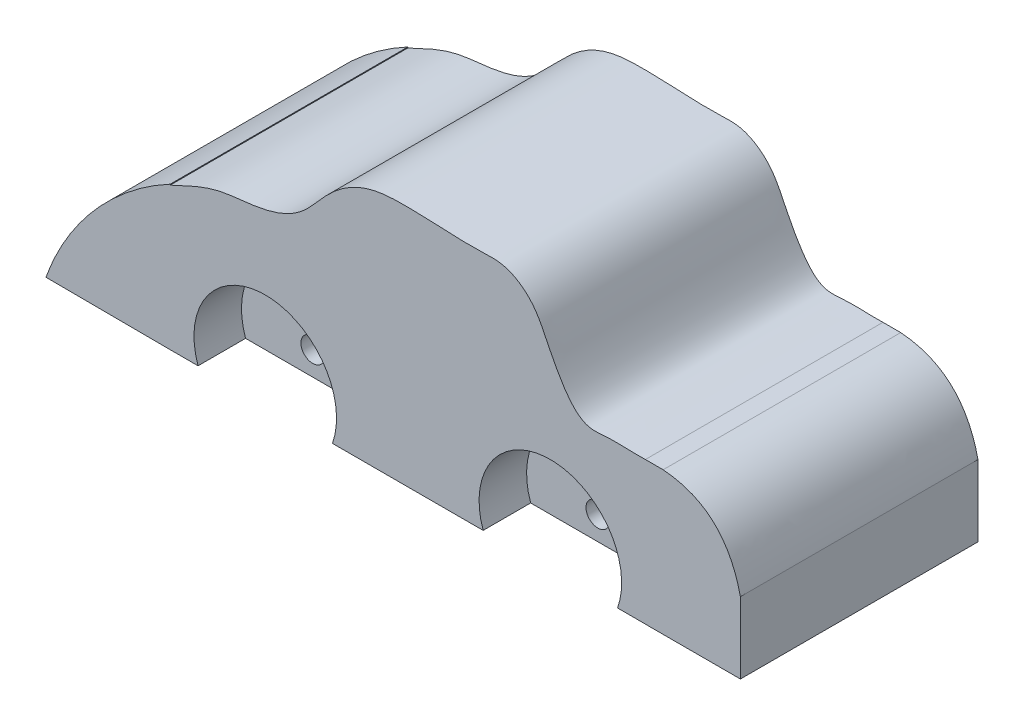
SolidWorks part; units mm, degrees
ref_plane "Front Plane" through (0, 0, 0) normal (0, 0, 1) x (1, 0, 0)
ref_plane "Top Plane" through (0, 0, 0) normal (0, 1, 0) x (1, 0, 0)
ref_plane "Right Plane" through (0, 0, 0) normal (1, 0, 0) x (0, 0, -1)
sketch "Sketch1" plane through (0, 0, 0) normal (0, 1, 0) x (1, 0, 0)
  line L1 (127, -63.5) -> (-127, -63.5)
  line L2 (127, -63.5) -> (127, 63.5)
  line L3 (127, 63.5) -> (-127, 63.5)
  line L4 (-127, -63.5) -> (-127, 63.5)
  line L5 (127, -63.5) -> (-127, 63.5) construction
  line L6 (127, 63.5) -> (-127, -63.5) construction
  point P0 (0, 0)
  dimension "D1" = 254
  dimension "D2" = 127
extrude "Boss-Extrude1" add sketch "Sketch1" along normal blind 152.4
sketch "Sketch3" plane through (0, 0, 0) normal (0, 0, 1) x (1, 0, 0)
  line L0 (-127, 152.4) -> (-127, 0) construction
  line L1 (127, 152.4) -> (127, 0) construction
  line L2 (-127, 76.2) -> (-127, 152.4)
  line L3 (-127, 152.4) -> (127, 152.4)
  line L4 (127, 152.4) -> (127, 76.2)
  spline S0 degree 3 poles (-127, 76.2) (-118.707, 80.0414) (-105.3738, 86.884) (-84.8438, 88.4889) (-68.8725, 91.348) (-55.8472, 98.9598) (-46.7117, 109.9524) (-36.2527, 120.8859) (-19.6372, 129.2056) (-1.4566, 129.7619) (18.361, 128.979) (34.9562, 128.0964) (53.2668, 129.4306) (67.0333, 119.9135) (74.4822, 104.3063) (81.7891, 89.5748) (92.7501, 74.7042) (110.2564, 76.936) (119.9392, 75.9846) (127, 76.2) knots 0 0 0 0 0.094545 0.14855 0.209484 0.258966 0.298587 0.355005 0.412691 0.482946 0.537791 0.615881 0.653229 0.722675 0.768672 0.828274 0.897984 0.928534 1 1 1 1
extrude "Cut-Extrude1" cut sketch "Sketch3" against normal blind 152.4 and the other way blind 152.4 contours L4 S0 L2 L3
sketch "Sketch4" plane through (0, 0, 0) normal (0, 0, 1) x (1, 0, 0)
  line L0 (-127, 0) -> (-76.2, 0) construction
  line L1 (-127, 0) -> (127, 0) construction
  line L2 (127, 0) -> (76.2, 0) construction
  line L3 (-76.2, 0) -> (-76.2, 12.7)
  line L4 (76.2, 0) -> (76.2, 12.7)
  dimension "D1" = 50.8
  dimension "D2" = 50.8
  dimension "D3" = 12.7
  dimension "D4" = 12.7
ref_plane "Plane3" through (0, 0, 63.5) normal (0, 0, 1) x (1, 0, 0)
sketch "Sketch5" plane through (0, 0, 63.5) normal (0, 0, 1) x (1, 0, 0)
  circle A0 centre (-76.2, 12.7) radius 38.1
  circle A1 centre (76.2, 12.7) radius 38.1
  dimension "D1" = 76.2
  dimension "D2" = 76.2
extrude "Cut-Extrude3" cut sketch "Sketch5" against normal blind 25.4
ref_plane "Plane4" through (0, 0, -63.5) normal (0, 0, 1) x (1, 0, 0)
sketch "Sketch6" plane through (0, 0, -63.5) normal (0, 0, -1) x (-1, 0, 0)
  circle A0 centre (-76.2, 12.7) radius 38.1
  circle A1 centre (76.2, 12.7) radius 38.1
  dimension "D1" = 76.2
  dimension "D2" = 76.2
extrude "Cut-Extrude4" cut sketch "Sketch6" against normal blind 25.4
sketch "Sketch7" plane through (0, 0, 38.1) normal (0, 0, 1) x (1, 0, 0)
  circle A0 centre (-76.2, 12.7) radius 6.35
  circle A1 centre (76.2, 12.7) radius 6.35
  dimension "D1" = 12.7
  dimension "D2" = 12.7
extrude "Cut-Extrude5" cut sketch "Sketch7" against normal blind 127 and the other way blind 25.4
ref_plane "Plane5" through (-127, 0, 0) normal (-1, 0, 0) x (0, 0, 1)
sketch "Sketch8" plane through (-127, 0, 0) normal (-1, 0, 0) x (0, 0, 1)
  line L0 (-63.5, 0) -> (63.5, 0)
  line L1 (-63.5, 0) -> (-63.5, 76.6671)
  line L2 (63.5, 0) -> (63.5, 76.6671)
  line L3 (-63.5, 76.6671) -> (63.5, 76.6671)
sketch "Sketch9" plane through (-127, 0, 0) normal (-1, 0, 0) x (0, 0, 1)
  line L0 (0, 76.2) -> (0, 0) construction
  line L1 (63.5, 76.2) -> (-63.5, 76.2) construction
ref_plane "Plane6" through (0, 0, 0) normal (0, 0, -1) x (0, -1, 0)
sketch "Sketch10" plane through (0, 0, 0) normal (0, 0, -1) x (0, -1, 0)
  spline S0 degree 3 poles (-76.2, 127) (-60.0589, 157.1369) (-32.3697, 181.7536) (0, 193.0877) knots 0 0 0 0 1 1 1 1
sweep "Sweep2" add profiles "Sketch8" path "Sketch10"
sketch "Sketch11" plane through (0, 0, -63.5) normal (0, 0, -1) x (-1, 0, 0)
  line L0 (127, 0) -> (193.4035, 0.3443)
  line L1 (127, 0) -> (127.3414, -65.8431)
  line L2 (193.4035, 0.3443) -> (193.7448, -65.4988)
  line L3 (127.3414, -65.8431) -> (193.7448, -65.4988)
extrude "Cut-Extrude6" cut sketch "Sketch11" against normal blind 127
sketch "Sketch12" plane through (-127, 0, 0) normal (-1, 0, 0) x (0, 0, 1)
  line L0 (63.5, 76.2) -> (-63.5, 76.3604)
  line L1 (63.5, 76.2) -> (63.4035, -0.1974)
  line L2 (-63.5, 76.3604) -> (-63.5965, -0.037)
  line L3 (63.4035, -0.1974) -> (-63.5965, -0.037)
ref_plane "Plane7" through (127, 0, 0) normal (1, 0, 0) x (0, 0, -1)
sketch "Sketch13" plane through (127, 0, 0) normal (1, 0, 0) x (0, 0, -1)
  line L0 (-63.5, 76.2) -> (63.5, 76.2)
  line L1 (-63.5, 76.2) -> (-63.5, -0.0371)
  line L2 (63.5, 76.2) -> (63.5, -0.0371)
  line L3 (-63.5, -0.0371) -> (63.5, -0.0371)
extrude "Boss-Extrude2" add sketch "Sketch13" along normal blind 50.8
sketch "Sketch15" plane through (0, 0, 0) normal (0, 0, 1) x (1, 0, 0)
  line L0 (177.8, 76.2) -> (177.8, -0.0371) construction
  line L1 (177.8, 38.0815) -> (177.8, 95.066)
  line L2 (177.8, 95.066) -> (124.755, 76.1588)
  spline S0 degree 2 poles (124.755, 76.1588) (168.4122, 79.4899) (177.8, 38.0815) knots 0 0 0 1 1 1
  spline S1 degree 3 poles (-127, 76.2) (-118.707, 80.0414) (-105.3738, 86.884) (-84.8438, 88.4889) (-68.8725, 91.348) (-55.8472, 98.9598) (-46.7117, 109.9524) (-36.2527, 120.8859) (-19.6372, 129.2056) (-1.4566, 129.7619) (18.361, 128.979) (34.9562, 128.0964) (53.2668, 129.4306) (67.0333, 119.9135) (74.4822, 104.3063) (81.7891, 89.5748) (92.7501, 74.7042) (110.2564, 76.936) (119.9392, 75.9846) (127, 76.2) knots 0 0 0 0 0.094545 0.14855 0.209484 0.258966 0.298587 0.355005 0.412691 0.482946 0.537791 0.615881 0.653229 0.722675 0.768672 0.828274 0.897984 0.928534 1 1 1 1 construction
extrude "Cut-Extrude7" cut sketch "Sketch15" against normal blind 127 and the other way blind 127
sketch "Sketch16" plane through (0, 0, 0) normal (0, 1, 0) x (1, 0, 0)
  line L0 (0, -63.5) -> (0, 63.5) construction
  line L1 (-40.279, -63.5) -> (40.279, -63.5) construction
  line L2 (40.279, 63.5) -> (-40.279, 63.5) construction
  line L3 (-193.4035, 0) -> (177.8, 0) construction
  line L4 (-193.4035, -63.5) -> (-193.4035, 63.5) construction
  line L5 (177.8, -63.5) -> (177.8, 63.5) construction
  line L7 (38.1, 12.7) -> (-38.1, 12.7)
  line L8 (38.1, 12.7) -> (38.1, -12.7)
  line L9 (38.1, -12.7) -> (-38.1, -12.7)
  line L10 (-38.1, 12.7) -> (-38.1, -12.7)
  line L11 (38.1, 12.7) -> (-38.1, -12.7) construction
  line L12 (38.1, -12.7) -> (-38.1, 12.7) construction
  point P12 (0, 0)
  dimension "D1" = 76.2
  dimension "D2" = 25.4
extrude "Cut-Extrude8" cut sketch "Sketch16" along normal blind 50.8
sketch "Sketch17" plane through (0, 0, 0) normal (0, 1, 0) x (1, 0, 0)
  line L0 (38.1, 0) -> (25.4, 0) construction
  line L1 (38.1, -12.7) -> (38.1, 12.7) construction
  line L2 (38.1, 12.7) -> (-38.1, 12.7) construction
  line L3 (33.6135, 25.4) -> (8.2135, 25.4)
  line L4 (33.6135, 25.4) -> (33.6135, -25.4)
  line L5 (33.6135, -25.4) -> (8.2135, -25.4)
  line L6 (8.2135, 25.4) -> (8.2135, -25.4)
  line L7 (33.6135, 25.4) -> (8.2135, -25.4) construction
  line L8 (33.6135, -25.4) -> (8.2135, 25.4) construction
  point P5 (20.9135, 0)
  dimension "D1" = 12.7
  dimension "D2" = 25.4
  dimension "D3" = 50.8
  dimension "D4" = 12.7
  dimension "D5" = 8.2135
extrude "Cut-Extrude12" cut sketch "Sketch17" along normal blind 50.8
equation "\"height\" = 2"
equation "\"width\"= 1"
equation "\"depth\"= 2"
equation "\"D1@Cut-Extrude8\"=\"depth\""
equation "\"encoderdepth\"= 0"
equation "\"D1@Cut-Extrude12\" = \"encoderdepth\""
